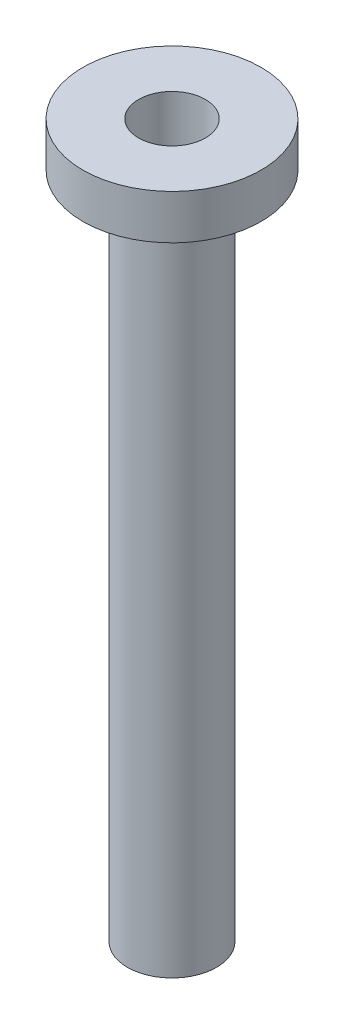
SolidWorks part; units mm, degrees
ref_plane "Front Plane" through (0, 0, 0) normal (0, 0, 1) x (1, 0, 0)
ref_plane "Top Plane" through (0, 0, 0) normal (0, 1, 0) x (1, 0, 0)
ref_plane "Right Plane" through (0, 0, 0) normal (1, 0, 0) x (0, 0, -1)
sketch "Sketch1" plane through (0, 0, 0) normal (0, 0, 1) x (1, 0, 0)
  line L0 (0, 0) -> (0, -101.6)
  line L3 (0, -101.6) -> (-6.35, -101.6)
  line L4 (-6.35, -101.6) -> (-6.35, -6.35)
  line L5 (-6.35, -6.35) -> (-12.7, -6.35)
  line L6 (-12.7, -6.35) -> (-12.7, 0)
  line L7 (-12.7, 0) -> (0, 0)
  dimension "D1" = 6.35
  dimension "D2" = 6.35
  dimension "D3" = 6.35
  dimension "D4" = 101.6
revolve "Revolve1" add sketch "Sketch1" angle 360 about L0
hole_wizard "3/8 (0.375) Diameter Hole1" positions "Sketch2" profile "Sketch4" hole size "3/8" standard "ANSI Inch"
sketch "Sketch2" plane through (0, 0, 0) normal (0, 1, 0) x (1, 0, 0)
  point P0 (0, 0)
sketch "Sketch4" plane through (0, 0, 0) normal (1, 0, 0) x (0, 0, 1)
  line L0 (0, 0) -> (0, 98.1116)
  line L1 (0, 98.1116) -> (4.7625, 95.25)
  line L2 (4.7625, 95.25) -> (4.7625, 0)
  line L5 (4.7625, 0) -> (0, 0)
  line L10 (0, 98.1116) -> (-4.7625, 95.25) construction
  line L11 (0, -6.35) -> (0, 107.95) construction
  dimension "Hole Dia." = 9.525
  dimension "Hole Depth" = 95.25
  dimension "Drill Angle" = 118
